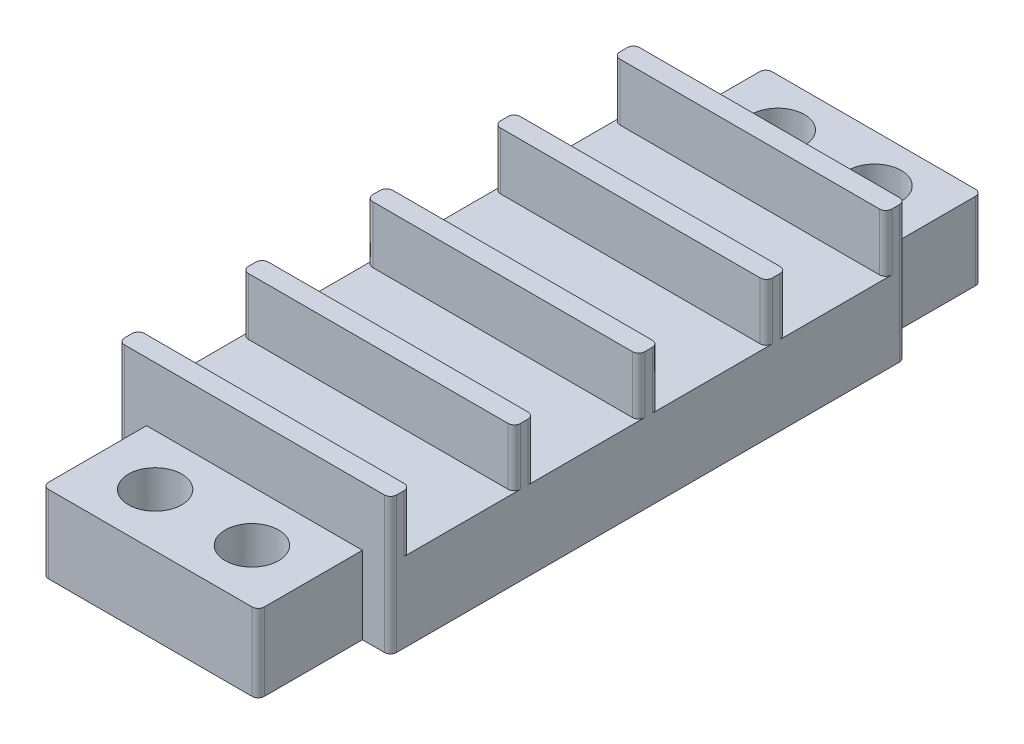
SolidWorks part; units mm, degrees
ref_plane "Front Plane" through (0, 0, 0) normal (0, 0, 1) x (1, 0, 0)
ref_plane "Top Plane" through (0, 0, 0) normal (0, 1, 0) x (1, 0, 0)
ref_plane "Right Plane" through (0, 0, 0) normal (1, 0, 0) x (0, 0, -1)
sketch "Sketch1" plane through (0, 0, 0) normal (0, 1, 0) x (1, 0, 0)
  line L1 (10.965, -20.76) -> (-10.965, -20.76)
  line L2 (10.965, -20.76) -> (10.965, 20.76)
  line L3 (10.965, 20.76) -> (-10.965, 20.76)
  line L4 (-10.965, -20.76) -> (-10.965, 20.76)
  line L5 (10.965, -20.76) -> (-10.965, 20.76) construction
  line L6 (10.965, 20.76) -> (-10.965, -20.76) construction
  point P0 (0, 0)
  dimension "D1" = 21.93
  dimension "D2" = 41.52
extrude "Boss-Extrude2" add sketch "Sketch1" along normal blind 11 contours L4 L3 L2 L1
sketch "Sketch3" plane through (0, 11, 0) normal (0, 1, 0) x (1, 0, 0)
  line L0 (0, -6.05) -> (0, 6.05) construction
  line L1 (10.965, -19.16) -> (-10.965, -19.16)
  line L2 (10.965, -19.16) -> (10.965, -10.78)
  line L3 (10.965, -10.78) -> (-10.965, -10.78)
  line L4 (-10.965, -19.16) -> (-10.965, -10.78)
  line L5 (10.965, -19.16) -> (-10.965, -10.78) construction
  line L6 (10.965, -10.78) -> (-10.965, -19.16) construction
  line L7 (-10.965, -20.76) -> (-10.965, 20.76) construction
  line L8 (10.965, -20.76) -> (-10.965, -20.76) construction
  line L9 (10.965, -9.18) -> (-10.965, -9.18)
  line L10 (10.965, -9.18) -> (10.965, -0.7573)
  line L11 (10.965, -0.7573) -> (-10.965, -0.7573)
  line L12 (-10.965, -9.18) -> (-10.965, -0.7573)
  line L13 (10.965, 0.8427) -> (-10.965, 0.8427)
  line L14 (10.965, 0.8427) -> (10.965, 9.5375)
  line L15 (10.965, 9.5375) -> (-10.965, 9.5375)
  line L16 (-10.965, 0.8427) -> (-10.965, 9.5375)
  line L17 (11.014, 11.1375) -> (-10.986, 11.1375)
  line L18 (11.014, 11.1375) -> (11.014, 19.16)
  line L19 (11.014, 19.16) -> (-10.986, 19.16)
  line L20 (-10.986, 11.1375) -> (-10.986, 19.16)
  line L21 (10.965, 20.76) -> (-10.965, 20.76) construction
  point P0 (0, -14.97)
  dimension "D1" = 8.38
  dimension "D2" = 1.6
  dimension "D3" = 1.6
  dimension "D4" = 1.6
  dimension "D5" = 1.6
  dimension "D6" = 1.6
  dimension "D7" = 22
extrude "Cut-Extrude2" cut sketch "Sketch3" against normal blind 4.6
sketch "Sketch5" plane through (0, 0, 0) normal (0, 0, 1) x (1, 0, 0)
  line L0 (-10.965, 11) -> (-10.965, 0) construction
  line L1 (-8.7, 6.2502) -> (8.7, 6.2502)
  line L2 (-8.7, 6.2502) -> (-8.7, 0.0002)
  line L3 (-8.7, 0.0002) -> (8.7, 0.0002)
  line L4 (8.7, 6.2502) -> (8.7, 0.0002)
  line L5 (-8.7, 6.2502) -> (8.7, 0.0002) construction
  line L6 (-8.7, 0.0002) -> (8.7, 6.2502) construction
  point P0 (0, 3.1252)
  dimension "D1" = 6.25
  dimension "D2" = 17.4
  dimension "D3" = 2.265
extrude "Boss-Extrude3" add sketch "Sketch5" along normal blind 8.4 from surface at 20.76 starting at face at (0, 5.5, 20.76)
sketch "Sketch6" plane through (0, 6.2502, 0) normal (0, 1, 0) x (1, 0, 0)
  line L0 (-8.7, -29.16) -> (-8.7, -20.76) construction
  line L1 (8.7, -29.16) -> (8.7, -20.76) construction
  circle A0 centre (-3.9, -24.8671) radius 2.15
  circle A1 centre (3.9, -24.8671) radius 2.15
  dimension "D1" = 4.8
  dimension "D2" = 4.8
extrude "Cut-Extrude3" cut sketch "Sketch6" against normal blind 8.4
sketch "Sketch7" plane through (0, 0, -20.76) normal (0, 0, -1) x (-1, 0, 0)
  line L0 (0, 6.05) -> (0, -6.05) construction
  line L1 (8.7, 0.0038) -> (-8.7, 0.0038)
  line L2 (8.7, 0.0038) -> (8.7, 6.2538)
  line L3 (8.7, 6.2538) -> (-8.7, 6.2538)
  line L4 (-8.7, 0.0038) -> (-8.7, 6.2538)
  line L5 (8.7, 0.0038) -> (-8.7, 6.2538) construction
  line L6 (8.7, 6.2538) -> (-8.7, 0.0038) construction
  point P0 (0, 3.1288)
  dimension "D1" = 17.4
  dimension "D2" = 6.25
extrude "Boss-Extrude4" add sketch "Sketch7" along normal blind 8.4
sketch "Sketch9" plane through (0, 6.2538, 0) normal (0, 1, 0) x (1, 0, 0)
  line L0 (-8.7, 29.16) -> (-8.7, 20.76) construction
  line L1 (8.7, 29.16) -> (8.7, 20.76) construction
  circle A0 centre (-3.9, 25.3263) radius 2.15
  circle A1 centre (3.9, 25.3263) radius 2.15
  dimension "D1" = 4.3
  dimension "D2" = 4.8
  dimension "D3" = 4.8
extrude "Cut-Extrude4" cut sketch "Sketch9" against normal blind 6.25
fillet "Fillet2" radius 0.5 24 edges at (-10.965, 8.7, 19.16) (10.965, 8.7, 19.16) (10.965, 8.7, 9.18) (10.965, 8.7, 10.78) (-10.965, 8.7, 9.18) (-10.965, 8.7, 10.78) (10.965, 8.7, -0.8427) (10.965, 8.7, 0.7573) (-10.965, 8.7, -0.8427) (-10.965, 8.7, 0.7573) (10.965, 8.7, -11.1375) (10.965, 8.7, -9.5375) (-10.965, 8.7, -9.5375) (-10.965, 8.7, -11.1375) (-10.965, 5.5, -20.76) (-10.965, 8.7, -19.16) (10.965, 8.7, -19.16) (10.965, 5.5, -20.76) (8.7, 3.1288, -29.16) (-8.7, 3.1288, -29.16) (-10.965, 5.5, 20.76) (10.965, 5.5, 20.76) (8.7, 3.1252, 29.16) (-8.7, 3.1252, 29.16)
